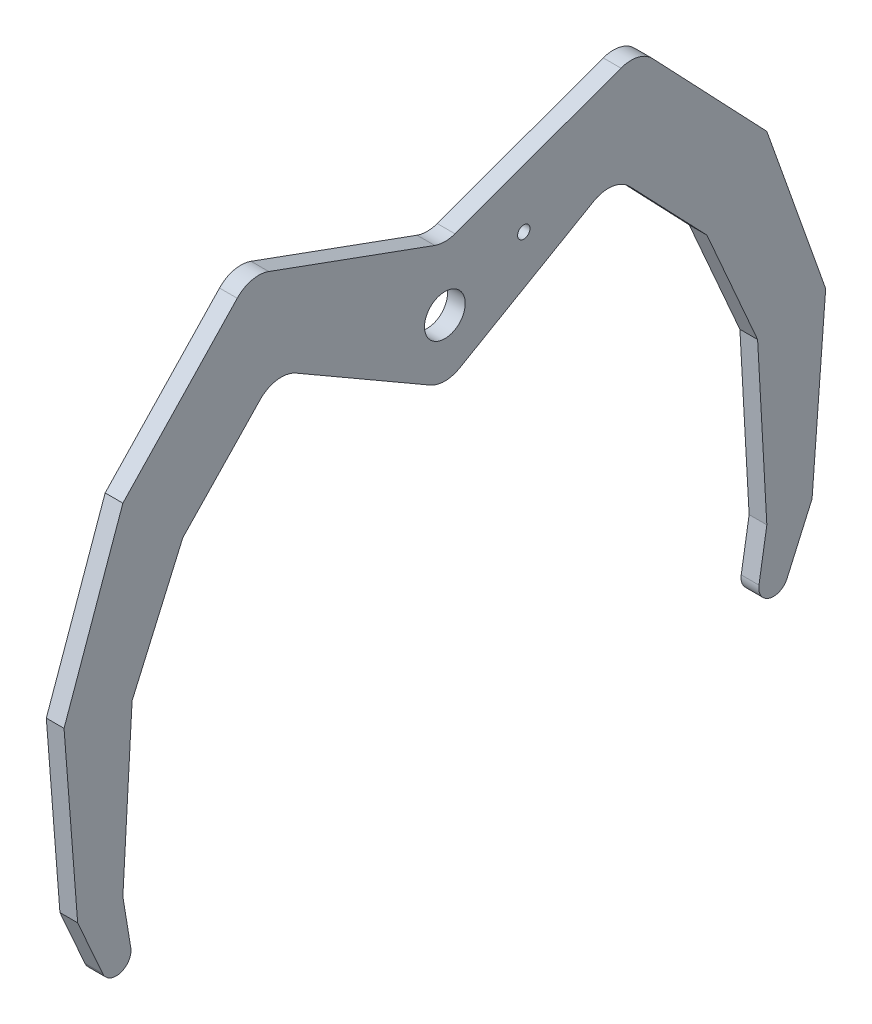
SolidWorks part; units mm, degrees
ref_plane "Front Plane" through (0, 0, 0) normal (0, 0, 1) x (1, 0, 0)
ref_plane "Top Plane" through (0, 0, 0) normal (0, 1, 0) x (1, 0, 0)
ref_plane "Right Plane" through (0, 0, 0) normal (1, 0, 0) x (0, 0, -1)
sketch "Sketch1" plane through (0, 0, 0) normal (1, 0, 0) x (0, 0, -1)
  line L0 (0, 15.8908) -> (0, -85.45) construction
  line L1 (1.7101, 11.0724) -> (29.8122, 21.3008)
  line L2 (2.5, -9.0066) -> (25.1791, 4.0871)
  line L3 (0, -85.45) -> (50, -85.45) construction
  line L4 (44.3608, -10.45) -> (31.2923, 3.213)
  line L5 (44.3608, -10.45) -> (52.94, -30.0455)
  line L6 (52.94, -30.0455) -> (54.5035, -58.0021)
  line L7 (54.5035, -58.0021) -> (53.1654, -66.1575)
  line L8 (-62.1586, -58.0021) -> (-64.4625, -28.3423)
  line L9 (-52.94, -30.0455) -> (-54.5035, -58.0021)
  line L10 (-64.4625, -28.3423) -> (-54.5035, -0.3096)
  line L11 (-44.3608, -10.45) -> (-52.94, -30.0455)
  line L12 (-44.3608, -10.45) -> (-31.2923, 3.213)
  line L13 (-54.5035, -0.3096) -> (-35.1457, 20.0478)
  line L14 (-2.5, -9.0066) -> (-25.1791, 4.0871)
  line L15 (-1.7101, 11.0724) -> (-29.8122, 21.3008)
  line L16 (62.1586, -58.0021) -> (57.9182, -67.5748)
  line L17 (62.1586, -58.0021) -> (64.4625, -28.3423)
  line L18 (64.4625, -28.3423) -> (54.5035, -0.3096)
  line L19 (54.5035, -0.3096) -> (35.1457, 20.0478)
  line L20 (-50.0689, 18.9616) -> (-69.3664, -3.6794) [skipped]
  line L21 (-69.3664, -3.6794) -> (-77.7866, -32.2121) [skipped]
  line L22 (-77.7866, -32.2121) -> (-73.8735, -61.7028) [skipped]
  line L23 (-73.8735, -61.7028) -> (-58.3038, -87.0523) [skipped]
  line L24 (-58.3038, -87.0523) -> (-33.7696, -103.8774) [skipped]
  line L25 (6.5074, 32.6053) -> (-8.3617, 32.2008) [skipped]
  line L26 (-23.2308, 31.7963) -> (-36.6498, 25.379) [skipped]
  line L27 (34.0036, 21.2488) -> (20.2555, 26.9271) [skipped]
  line L28 (24.407, -102.2948) -> (36.1986, -93.2277) [skipped]
  line L29 (-4.5131, -109.269) -> (9.947, -105.7819) [skipped]
  line L30 (-33.7696, -103.8774) -> (-4.5131, -109.269) [skipped]
  line L31 (-54.5035, -58.0021) -> (-53.1654, -66.1575)
  line L32 (-62.1586, -58.0021) -> (-57.9182, -67.5748)
  line L33 (57.1307, -67.2849) -> (62.1586, -58.0021) [skipped]
  line L34 (13.3577, 5.5112) -> (0, 0) construction
  circle A0 centre (0, 0) radius 3.45
  arc A1 (53.1654, -66.1575) -> (57.9182, -67.5748) centre (55.6324, -66.5622) ccw
  arc A2 (-29.8122, 21.3008) -> (-35.1457, 20.0478) centre (-31.5223, 16.6023) ccw
  arc A3 (-53.1654, -66.1575) -> (-57.9182, -67.5748) centre (-55.6324, -66.5622) cw
  arc A4 (29.8122, 21.3008) -> (35.1457, 20.0478) centre (31.5223, 16.6023) cw
  arc A5 (31.2923, 3.213) -> (25.1791, 4.0871) centre (27.6791, -0.243) ccw
  arc A6 (-31.2923, 3.213) -> (-25.1791, 4.0871) centre (-27.6791, -0.243) cw
  arc A7 (1.7101, 11.0724) -> (-1.7101, 11.0724) centre (0, 15.7709) cw
  arc A8 (-2.5, -9.0066) -> (2.5, -9.0066) centre (0, -4.6765) ccw
  circle A9 centre (13.3577, 5.5112) radius 1.05
  point P56 (28.5788, 6.05)
  point P59 (32.8892, 22.4207)
  point P64 (28.5788, 6.05)
  point P68 (0, 10.45)
  point P71 (0, -10.45)
  point P73 (-28.5788, 6.05)
  point P74 (0, -10.45)
  point P75 (0, -10.45)
  dimension "D1" = 5
  dimension "D10" = 14.45
  dimension "D6" = 2.5
  dimension "D7" = 5
  dimension "D11" = 6.9
  dimension "D12" = 2.1
  dimension "D2" = 70
  dimension "D3" = 60
  dimension "D4" = 35
  dimension "D5" = 33
  dimension "D8" = 50
  dimension "D9" = 75
extrude "Boss-Extrude1" add sketch "Sketch1" along normal blind 3
